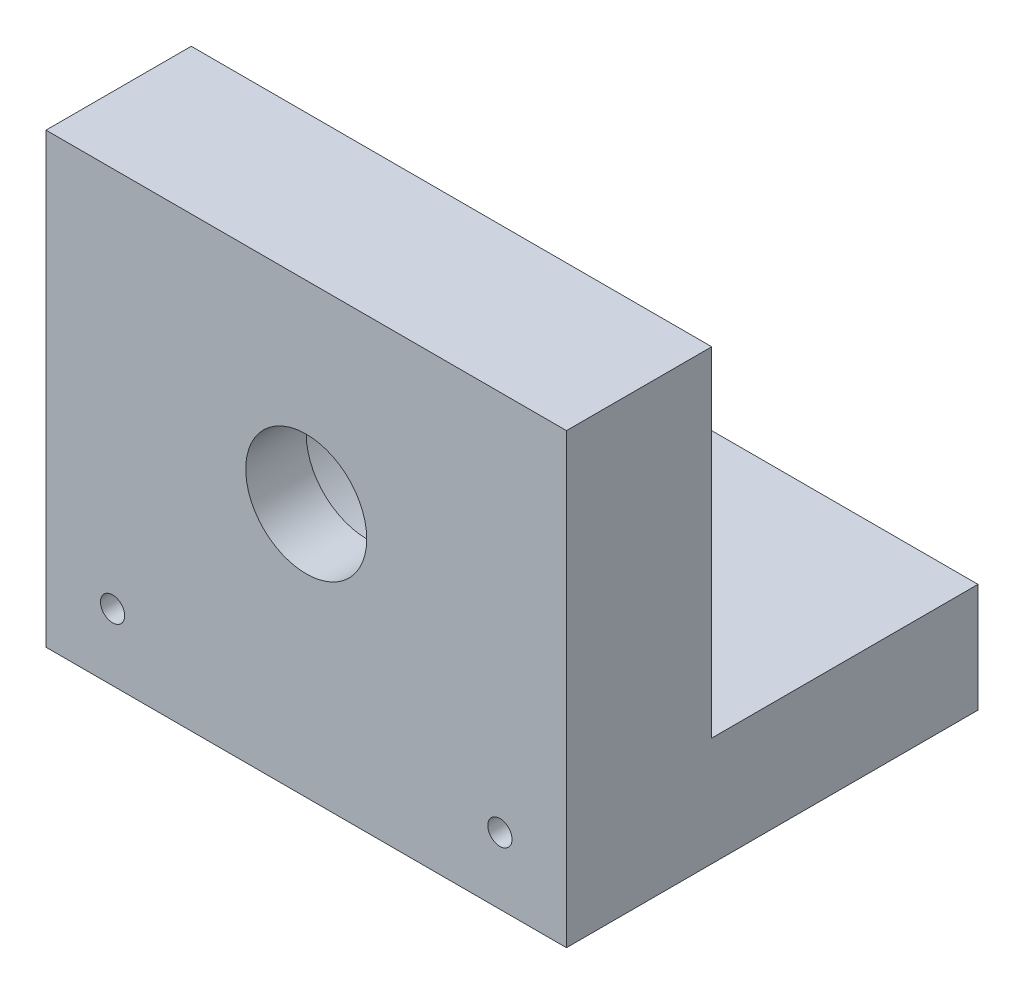
SolidWorks part; units mm, degrees
ref_plane "Front Plane" through (0, 0, 0) normal (0, 0, 1) x (1, 0, 0)
ref_plane "Top Plane" through (0, 0, 0) normal (0, 1, 0) x (1, 0, 0)
ref_plane "Right Plane" through (0, 0, 0) normal (1, 0, 0) x (0, 0, -1)
sketch "Sketch2" plane through (0, 0, 0) normal (0, 0, 1) x (1, 0, 0)
  line L0 (21.5, 0) -> (21.5, 21) construction
  line L1 (0, 0) -> (43, 0)
  line L2 (0, 0) -> (0, 37)
  line L3 (0, 37) -> (43, 37)
  line L4 (43, 0) -> (43, 37)
  circle A0 centre (21.5, 21) radius 5
  dimension "D3" = 10
  dimension "D1" = 21
  dimension "D2" = 43
  dimension "D4" = 37
extrude "Boss-Extrude1" add sketch "Sketch2" against normal blind 12
sketch "Sketch3" plane through (0, 0, -12) normal (0, 0, -1) x (-1, 0, 0)
  circle A0 centre (-21.5, 21) radius 11
  dimension "D1" = 22
extrude "Cut-Extrude1" cut sketch "Sketch3" against normal blind 7
sketch "Sketch4" plane through (0, 0, 0) normal (0, -1, 0) x (1, 0, 0)
  line L0 (0, 0) -> (43, 0) construction
  line L1 (0, 0) -> (43, 0)
  line L2 (0, 0) -> (0, -34)
  line L3 (0, -34) -> (43, -34)
  line L4 (43, 0) -> (43, -34)
  dimension "D1" = 34
extrude "Boss-Extrude2" add sketch "Sketch4" against normal blind 9
sketch "Sketch5" plane through (0, 0, 0) normal (0, 0, 1) x (1, 0, 0)
  line L0 (0, 0) -> (5.5, 0) construction
  line L1 (0, 0) -> (43, 0) construction
  line L2 (5.5, 0) -> (5.5, 5.5) construction
  line L3 (43, 0) -> (37.5, 0) construction
  line L4 (37.5, 0) -> (37.5, 5.5) construction
  circle A0 centre (5.5, 5.5) radius 1
  circle A1 centre (37.5, 5.5) radius 1
  dimension "D2" = 2
  dimension "D1" = 5.5
extrude "Cut-Extrude2" cut sketch "Sketch5" against normal blind 10
